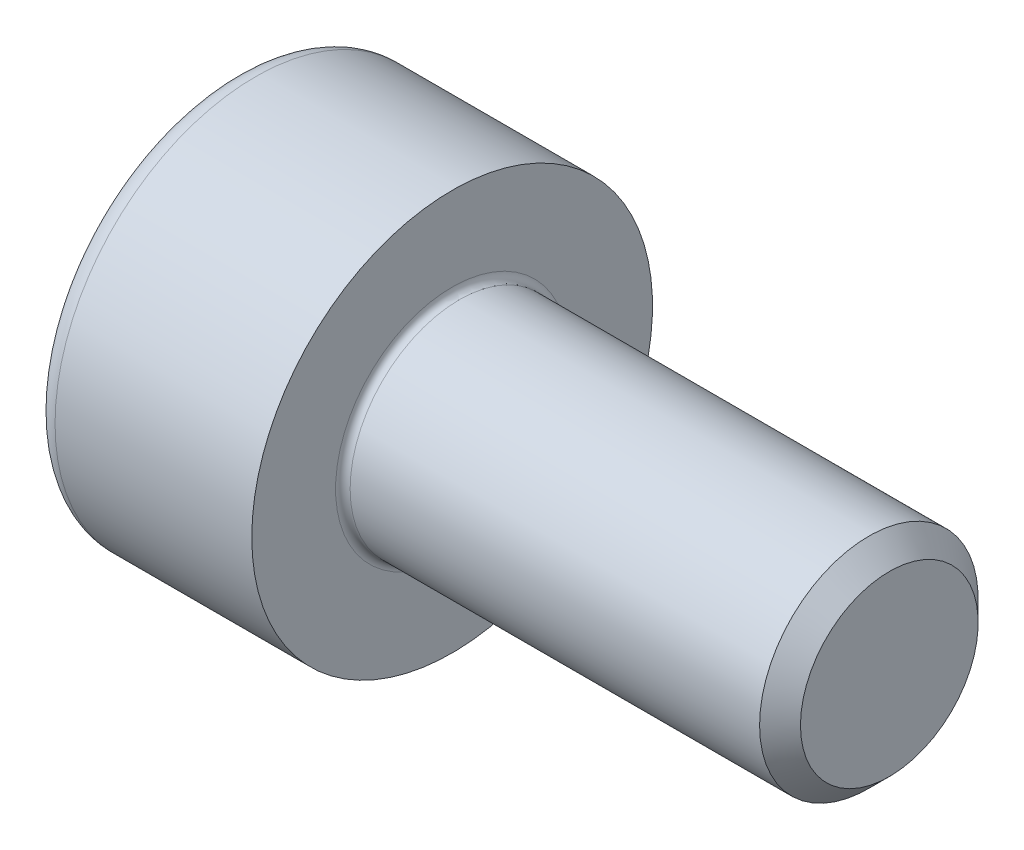
SolidWorks part; units mm, degrees
revolve "Base-Revolve" add sketch "BodySke"
sketch "BodySke" plane through (0, 0, 0) normal (0, 0, 1) x (1, 0, 0)
  line L0 (0, 0) -> (0, 2.75)
  line L1 (0, 2.75) -> (3, 2.75)
  line L2 (3, 2.75) -> (3, 1.5)
  line L3 (3, 1.5) -> (8.7195, 1.5)
  line L4 (9, 1.2195) -> (9, 0)
  line L5 (9, 0) -> (0, 0)
  line L6 (-31.75, 0) -> (127, 0) construction
  line L8 (9, 1.2195) -> (8.7195, 1.5)
  line L10 (9, -1.2195) -> (8.7195, -1.5) construction
  line L11 (3.5, 9.525) -> (3.5, 3.175) construction
  line L12 (3, 9.525) -> (3, 3.175) construction
  line L13 (-51, 9.525) -> (-51, 3.175) construction
  dimension "Head_ht" = 3
  dimension "Length" = 6
  dimension "Body_ch_ang" = 45
  dimension "Diameter" = 3
  dimension "Minor_dia" = 2.439
  dimension "Advance" = 0.5
  dimension "Thread_nom" = 6
  dimension "Thread_length" = 60
  dimension "Head_dia" = 5.5
cosmetic thread "ThreadCosmetic"
fillet "Fillet1" radius 0.1 1 edges at (3, 0, 1.5)
fillet "Fillet2" radius 0.3 1 edges at (0, 0, 2.75)
ref_plane "Plane1" through (0, 0, 0) normal (0, 0, 1) x (1, 0, 0)
ref_plane "Plane2" through (0, 0, 0) normal (0, 1, 0) x (1, 0, 0)
ref_plane "Plane3" through (0, 0, 0) normal (1, 0, 0) x (0, 0, -1)
sketch "Sketch2" plane through (0, 0, 0) normal (0, 0, 1) x (1, 0, 0)
  line L0 (0, 1.26) -> (1.3, 1.26)
  line L1 (1.3, 1.26) -> (2.0275, 0)
  line L2 (-31.75, 0) -> (127, 0) construction
  line L3 (2.0275, 0) -> (0, 0)
  line L4 (0, 0) -> (0, 1.26)
  line L6 (0, 0) -> (47.625, 0) construction
  dimension "D1" = 1.26
  dimension "D2" = 60
  dimension "Depth" = 1.3
revolve "Hex-PreBroach" cut sketch "Sketch2" angle 360 about L6
sketch "Sketch3" plane through (0, 0, 0) normal (-1, 0, 0) x (0, 0.5, 0.866)
  line L0 (0.7275, 1.26) -> (-0.7275, 1.26)
  line L1 (-0.7275, 1.26) -> (-1.4549, 0)
  line L2 (0.7275, 1.26) -> (1.4549, 0)
  line L3 (0.7275, -1.26) -> (1.4549, 0)
  line L4 (0.7275, -1.26) -> (-0.7275, -1.26)
  line L5 (-0.7275, -1.26) -> (-1.4549, 0)
  dimension "D1" = 1.26
  dimension "D2" = 1.26
  dimension "Hex_size" = 2.52
extrude "Hex" cut sketch "Sketch3" against normal blind 1.3
sketch "ThdSchSke" plane through (0, 0, 0) normal (0, 0, 1) x (1, 0, 0)
  line L0 (4.5, -1.2195) -> (4.3036, -1.5)
  line L1 (4.5, -1.2195) -> (4.6964, -1.5)
  line L2 (4.6964, -1.5) -> (4.6964, -1.875)
  line L3 (-3.175, 0) -> (5.1513, 0) construction
  line L4 (0, 2.45) -> (0, -2.45) construction
  line L5 (4.6964, -1.875) -> (4.3036, -1.875)
  line L6 (4.3036, -1.875) -> (4.3036, -1.5)
  dimension "Thread_minor" = 2.439
  dimension "Diameter" = 3
  dimension "Start" = 4.5
revolve "ThreadSchematic" [suppressed] cut sketch "ThdSchSke" angle 360 about L3
pattern_linear "ThdSchPat" [suppressed]
equation "\"D2@Sketch3\" = \"Hex_size@Sketch3\" / 2"
equation "\"D1@Sketch3\" = \"Hex_size@Sketch3\" / 2"
equation "\"D1@Sketch2\" = \"Hex_size@Sketch3\" / 2"
equation "\"Thread_minor@ThreadCosmetic\"  =  \"Minor_dia@BodySke\""
equation "\"Depth@Sketch2\" =  \"Key_eng@Hex\""
equation "\"Thread_length@ThreadCosmetic\" = ((sgn( (\"Length@BodySke\" - \"Advance@BodySke\" * 3.0) - \"Thread_nom@BodySke\" )-1)*( (\"Length@BodySke\" - \"Advance@BodySke\" * 3.0) - \"Thread_nom@BodySke\" ))/-2+ \"Thread_nom@BodySke\""
equation "\"Thread_minor@ThdSchSke\" = \"Minor_dia@BodySke\""
equation "\"Diameter@ThdSchSke\" = \"Diameter@BodySke\""
equation "\"Overcut@ThdSchSke\" = \"Diameter@BodySke\" * 1.25"
equation "\"Start@ThdSchSke\" = \"Head_ht@BodySke\" + \"Length@BodySke\" - \"Thread_length@ThreadCosmetic\"  '---Non-countersunk---"
equation "\"Num_threads@ThdSchPat\" = int( \"Thread_length@ThreadCosmetic\" / \"Advance@BodySke\" + 0.999 )  + 1"
equation "\"Advance@ThdSchPat\" = \"Thread_length@ThreadCosmetic\" /  (\"Num_threads@ThdSchPat\" - 1) 'relax it"
equation "\"Num_threads@ThdSchPat\" = \"Num_threads@ThdSchPat\" - sgn( \"Num_threads@ThdSchPat\" - 1) '---chamfered tips only---"
